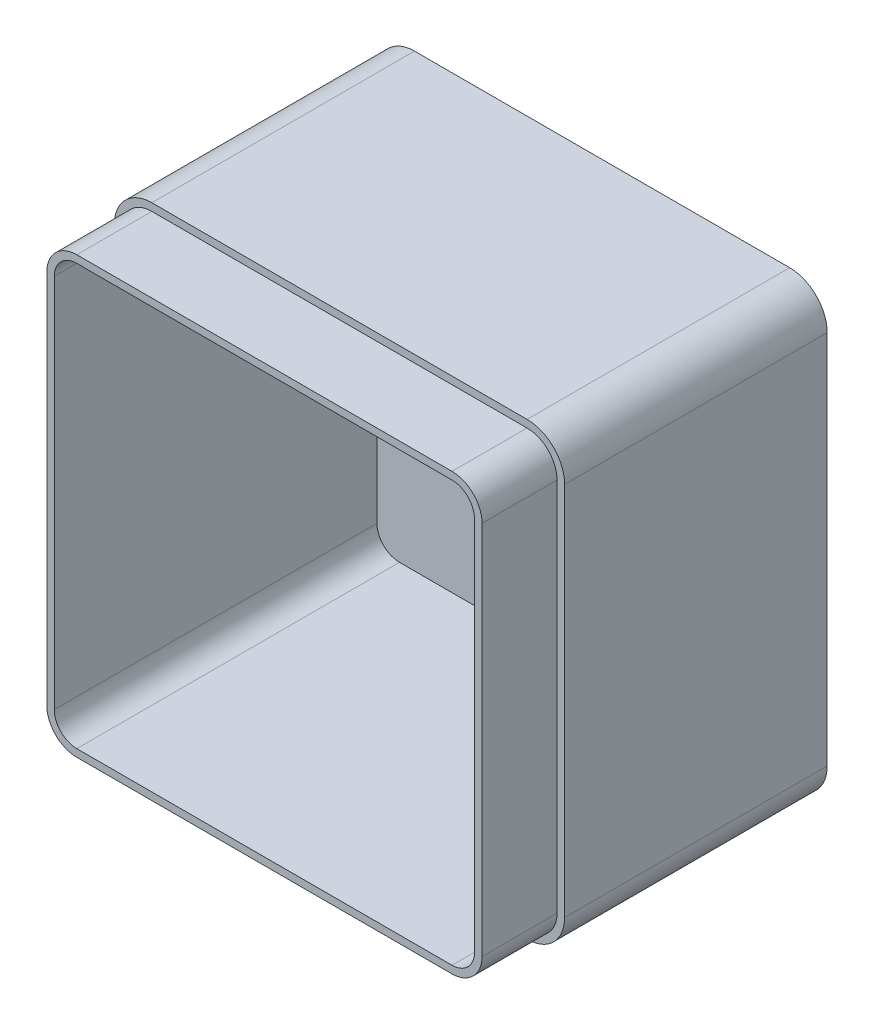
SolidWorks part; units mm, degrees
ref_plane "Front Plane" through (0, 0, 0) normal (0, 0, 1) x (1, 0, 0)
ref_plane "Top Plane" through (0, 0, 0) normal (0, 1, 0) x (1, 0, 0)
ref_plane "Right Plane" through (0, 0, 0) normal (1, 0, 0) x (0, 0, -1)
sketch "Sketch1" plane through (0, 0, 0) normal (0, 0, 1) x (1, 0, 0)
  line L1 (0, 0) -> (-120, 0)
  line L2 (0, 0) -> (0, 120)
  line L3 (0, 120) -> (-120, 120)
  line L4 (-120, 0) -> (-120, 120)
  dimension "D1" = 120
  dimension "D2" = 120
extrude "Boss-Extrude2" add sketch "Sketch1" along normal blind 70 contours L2 L1 L4 L3
fillet "Fillet2" radius 10 4 edges at (-120, 0, 35) (0, 0, 35) (-120, 120, 35) (0, 120, 35)
shell "Shell2" thickness 4
sketch3d "3DSketch3"
  line L0 (-2, 10, 70) -> (-2, 110, 70)
  line L1 (-10, 118, 70) -> (-110, 118, 70)
  line L2 (-118, 10, 70) -> (-118, 110, 70)
  line L3 (-10, 2, 70) -> (-110, 2, 70)
  line L4 (-2, 10, 70) -> (-2, 110, 70)
  line L5 (-10, 118, 70) -> (-110, 118, 70)
  line L6 (-118, 10, 70) -> (-118, 110, 70)
  line L7 (-10, 2, 70) -> (-110, 2, 70)
  arc A0 (-10, 2, 70) -> (-2, 10, 70) centre (-10, 10, 70) ccw
  arc A1 (-2, 110, 70) -> (-10, 118, 70) centre (-10, 110, 70) ccw
  arc A2 (-110, 118, 70) -> (-118, 110, 70) centre (-110, 110, 70) ccw
  arc A3 (-118, 10, 70) -> (-110, 2, 70) centre (-110, 10, 70) ccw
  arc A4 (-10, 2, 70) -> (-2, 10, 70) centre (-10, 10, 70) ccw
  arc A5 (-2, 110, 70) -> (-10, 118, 70) centre (-10, 110, 70) ccw
  arc A6 (-110, 118, 70) -> (-118, 110, 70) centre (-110, 110, 70) ccw
  arc A7 (-118, 10, 70) -> (-110, 2, 70) centre (-110, 10, 70) ccw
  point P3 (-10, 10, 78)
  point P7 (-10, 110, 78)
  point P11 (-110, 110, 78)
  point P15 (-110, 10, 78)
  point P16 (-10, 10, 78)
  point P17 (-10, 110, 78)
  point P18 (-110, 110, 78)
  point P19 (-110, 10, 78)
  dimension "D1" = 2
extrude "Boss-Extrude3" add sketch "3DSketch3" along direction (0, 0, -1) on the side against the normal blind 20
sketch3d "3DSketch4"
  line L0 (-4, 10, 90) -> (-4, 110, 90)
  line L1 (-10, 116, 90) -> (-110, 116, 90)
  line L2 (-116, 110, 90) -> (-116, 10, 90)
  line L3 (-110, 4, 90) -> (-10, 4, 90)
  line L4 (-4, 10, 90) -> (-4, 110, 90)
  line L5 (-10, 116, 90) -> (-110, 116, 90)
  line L6 (-116, 110, 90) -> (-116, 10, 90)
  line L7 (-110, 4, 90) -> (-10, 4, 90)
  arc A0 (-10, 4, 90) -> (-4, 10, 90) centre (-10, 10, 90) ccw
  arc A1 (-4, 110, 90) -> (-10, 116, 90) centre (-10, 110, 90) ccw
  arc A2 (-110, 116, 90) -> (-116, 110, 90) centre (-110, 110, 90) ccw
  arc A3 (-116, 10, 90) -> (-110, 4, 90) centre (-110, 10, 90) ccw
  arc A4 (-10, 4, 90) -> (-4, 10, 90) centre (-10, 10, 90) ccw
  arc A5 (-4, 110, 90) -> (-10, 116, 90) centre (-10, 110, 90) ccw
  arc A6 (-110, 116, 90) -> (-116, 110, 90) centre (-110, 110, 90) ccw
  arc A7 (-116, 10, 90) -> (-110, 4, 90) centre (-110, 10, 90) ccw
  point P3 (-10, 10, 96)
  point P7 (-10, 110, 96)
  point P11 (-110, 110, 96)
  point P15 (-110, 10, 96)
  point P16 (-10, 10, 96)
  point P17 (-10, 110, 96)
  point P18 (-110, 110, 96)
  point P19 (-110, 10, 96)
  dimension "D1" = 2
extrude "Cut-Extrude2" cut sketch "3DSketch4" along direction (0, 0, 1) on the side of the normal blind 40 contours A4 L4 A5 L5 A6 L6 A7 L7
